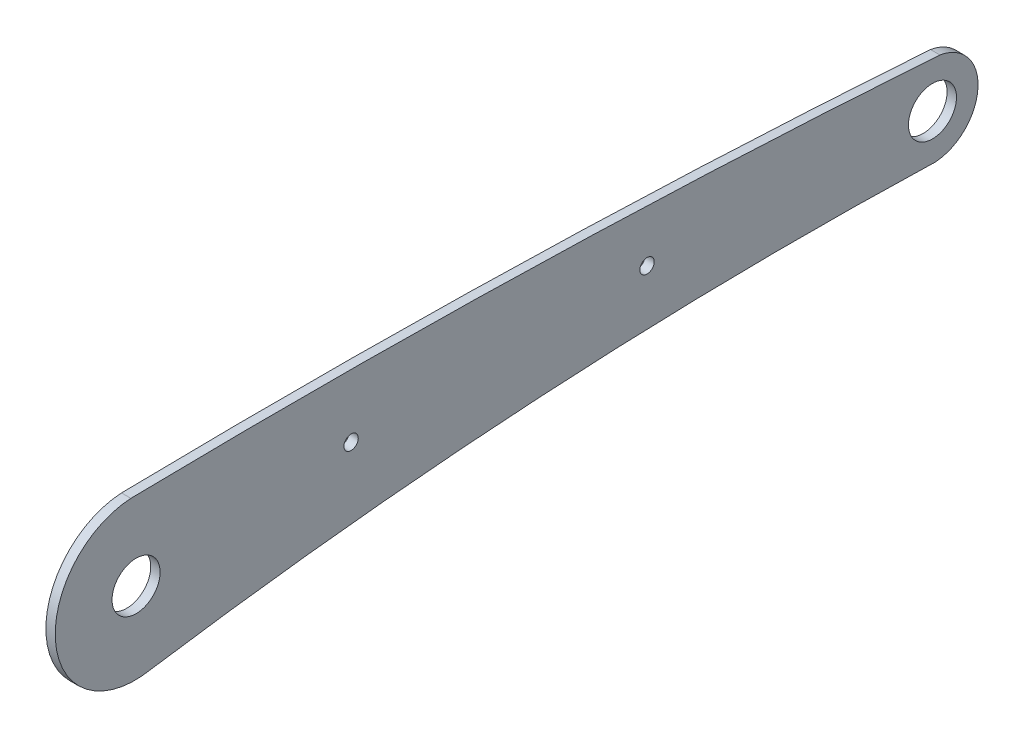
SolidWorks part; units mm, degrees
ref_plane "前基準面" through (0, 0, 0) normal (0, 0, 1) x (1, 0, 0)
ref_plane "上基準面" through (0, 0, 0) normal (0, 1, 0) x (1, 0, 0)
ref_plane "右基準面" through (0, 0, 0) normal (1, 0, 0) x (0, 0, -1)
sketch "草圖1" plane through (0, 0, 0) normal (1, 0, 0) x (0, 0, -1)
  circle A6 centre (66.6171, 2.1616) radius 3.85
  circle A7 centre (-60.9697, 0.0796) radius 3.85
  circle A8 centre (20.8921, 3.5712) radius 1.149
  circle A9 centre (-26.5219, 2.7975) radius 1.149
  arc A10 (66.5877, -5.1166) -> (-58.6335, -12.6811) centre (45.4653, -695.6897) ccw
  arc A11 (-61.804, 12.6555) -> (-58.6335, -12.6811) centre (-61.1216, -0.1258) ccw
  arc A12 (66.5877, -5.1166) -> (67.0956, -5.1266) centre (66.9001, -2.1485) ccw
  arc A13 (67.0956, -5.1266) -> (67.7985, 9.3693) centre (66.6171, 2.1616) ccw
  arc A14 (67.7985, 9.3693) -> (-61.804, 12.6555) centre (-33.8038, -1440.3614) ccw
  dimension "D1" = 7.7
  dimension "D3" = 7.7
  dimension "D2" = 127.5868
extrude "填料-伸長1" add sketch "草圖1" along normal blind 1.5
